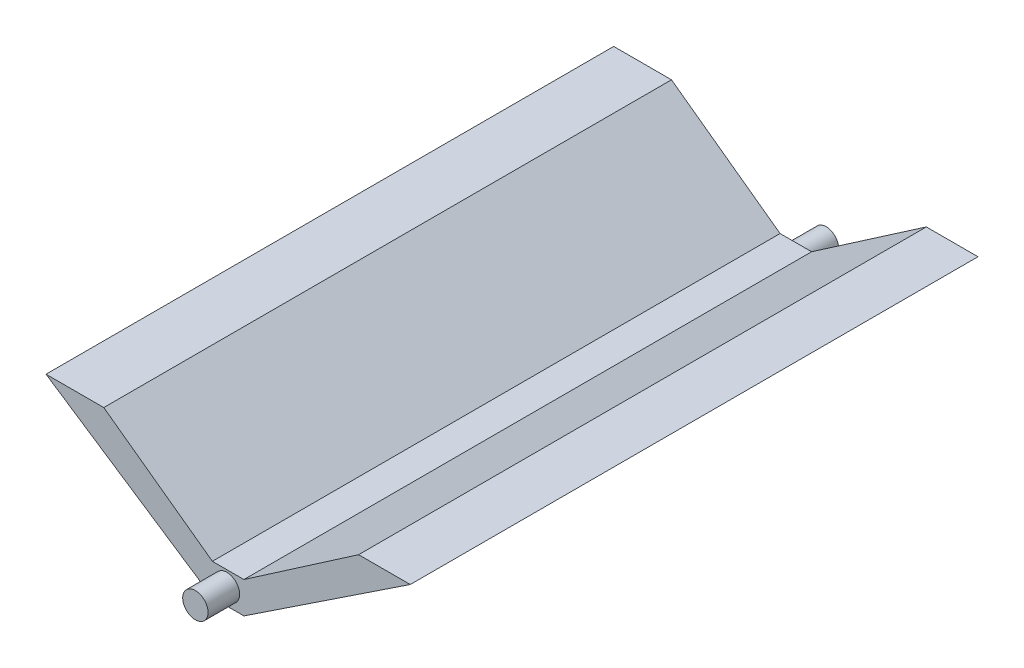
SolidWorks part; units mm, degrees
ref_plane "Front Plane" through (0, 0, 0) normal (0, 0, 1) x (1, 0, 0)
ref_plane "Top Plane" through (0, 0, 0) normal (0, 1, 0) x (1, 0, 0)
ref_plane "Right Plane" through (0, 0, 0) normal (1, 0, 0) x (0, 0, -1)
sketch "Sketch1" plane through (0, 0, 0) normal (0, 0, 1) x (1, 0, 0)
  line L1 (-115.5, 32.5936) -> (-10, -37.4064)
  line L2 (10, -37.4064) -> (-10, -37.4064)
  line L3 (115.5, 32.5936) -> (-115.5, 32.5936)
  line L4 (10, -37.4064) -> (115.5, 32.5936)
extrude "Boss-Extrude1" add sketch "Sketch1" along normal blind 360
sketch "Sketch2" plane through (0, 0, 360) normal (0, 0, 1) x (1, 0, 0)
  line L0 (-78.8671, 32.5936) -> (82.7331, 32.5936)
  line L1 (-10, -17.4064) -> (10, -17.4064)
  line L3 (-10, -17.4064) -> (-78.8671, 32.5936)
  line L4 (115.5, 32.5936) -> (-115.5, 32.5936) construction
  line L5 (10, -17.4064) -> (82.7331, 32.5936)
extrude "Cut-Extrude1" cut sketch "Sketch2" against normal blind 360
sketch "Sketch3" plane through (0, 0, 360) normal (0, 0, 1) x (1, 0, 0)
  circle A0 centre (-0.7732, -26.8913) radius 8.05
extrude "Boss-Extrude2" add sketch "Sketch3" along normal blind 20 contours A0
sketch "Sketch4" plane through (0, 0, 0) normal (0, 0, -1) x (-1, 0, 0)
  circle A0 centre (0.7732, -26.8913) radius 7.8738
extrude "Boss-Extrude3" add sketch "Sketch4" along normal blind 20
